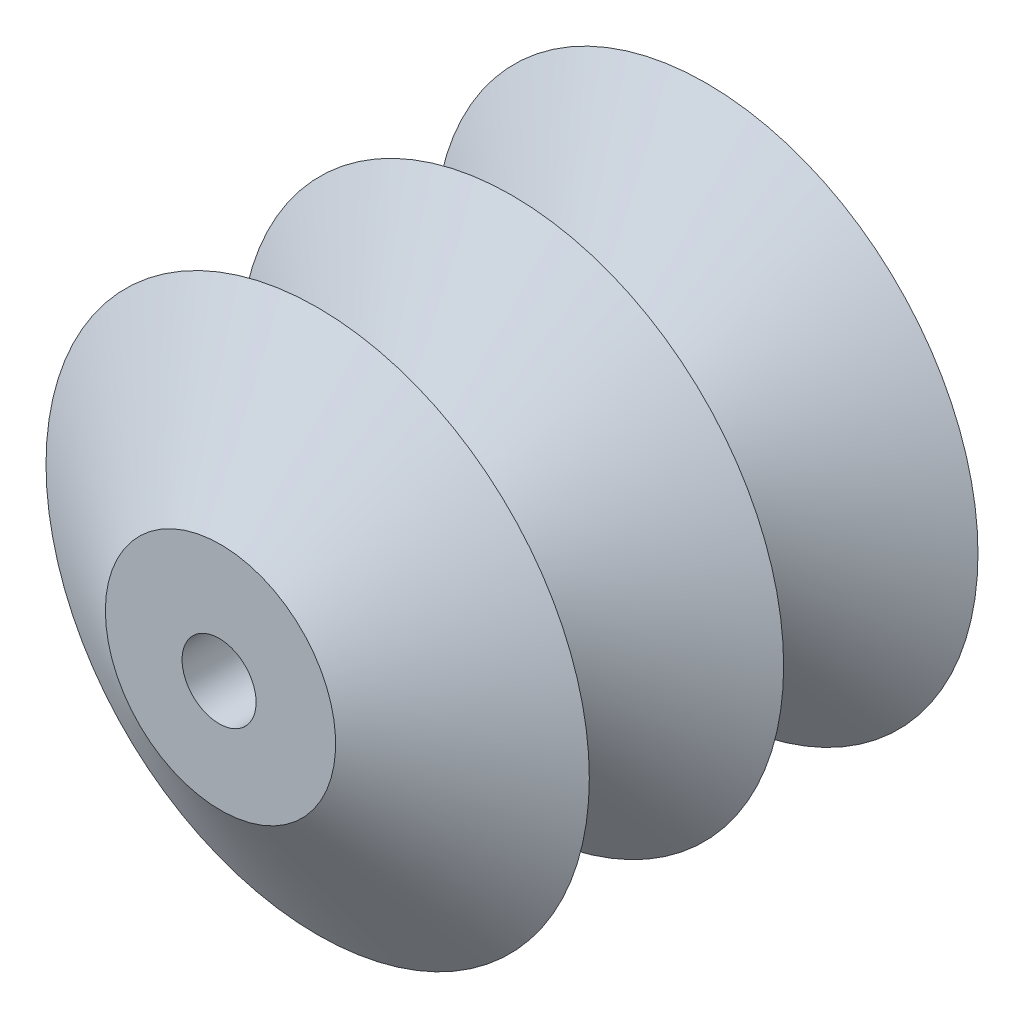
SolidWorks part; units mm, degrees
ref_plane "Front Plane" through (0, 0, 0) normal (0, 0, 1) x (1, 0, 0)
ref_plane "Top Plane" through (0, 0, 0) normal (0, 1, 0) x (1, 0, 0)
ref_plane "Right Plane" through (0, 0, 0) normal (1, 0, 0) x (0, 0, -1)
sketch "Croquis1" plane through (0, 0, 0) normal (0, 1, 0) x (1, 0, 0)
  line L0 (0, 35.4441) -> (0, -35.4441)
  line L1 (0, 35.4441) -> (14, 35.4441)
  line L2 (0, -35.4441) -> (14, -35.4441)
  line L3 (14, -35.4441) -> (33.0315, -23.6294)
  line L4 (33.0315, -23.6294) -> (14, -11.8147)
  line L5 (14, -11.8147) -> (33.0315, 0)
  line L6 (33.0315, 0) -> (14, 11.8147)
  line L7 (14, 11.8147) -> (33.0315, 23.6294)
  line L8 (33.0315, 23.6294) -> (14, 35.4441)
  point P4 (0, 0)
  point P12 (0, 0)
  point P13 (0, 0)
  point P14 (33.0315, 23.6294)
  dimension "D1" = 14
revolve "Revolución1" add sketch "Croquis1" angle 360 about L0
hole_wizard "Taladro de margen para M81" positions "Croquis3" profile "Croquis2" hole size "M8" standard "ISO" end condition through all
sketch "Croquis3" plane through (0, 0, 35.4441) normal (0, 0, 1) x (1, 0, 0)
  point P0 (-0.173, -0.4759)
sketch "Croquis2" plane through (-0.173, -0.4759, 35.4441) normal (1, 0, 0) x (0, -1, 0)
  line L0 (0, 0) -> (0, 70.8883)
  line L1 (0, 70.8883) -> (4.5, 70.8883)
  line L2 (4.5, 70.8883) -> (4.5, 0)
  line L5 (4.5, 0) -> (0, 0)
  line L11 (0, -6.35) -> (0, 107.95) construction
  dimension "Diámetro de taladro hasta el siguiente" = 9
  dimension "Profundidad de taladro hasta el siguiente" = 70.8883
